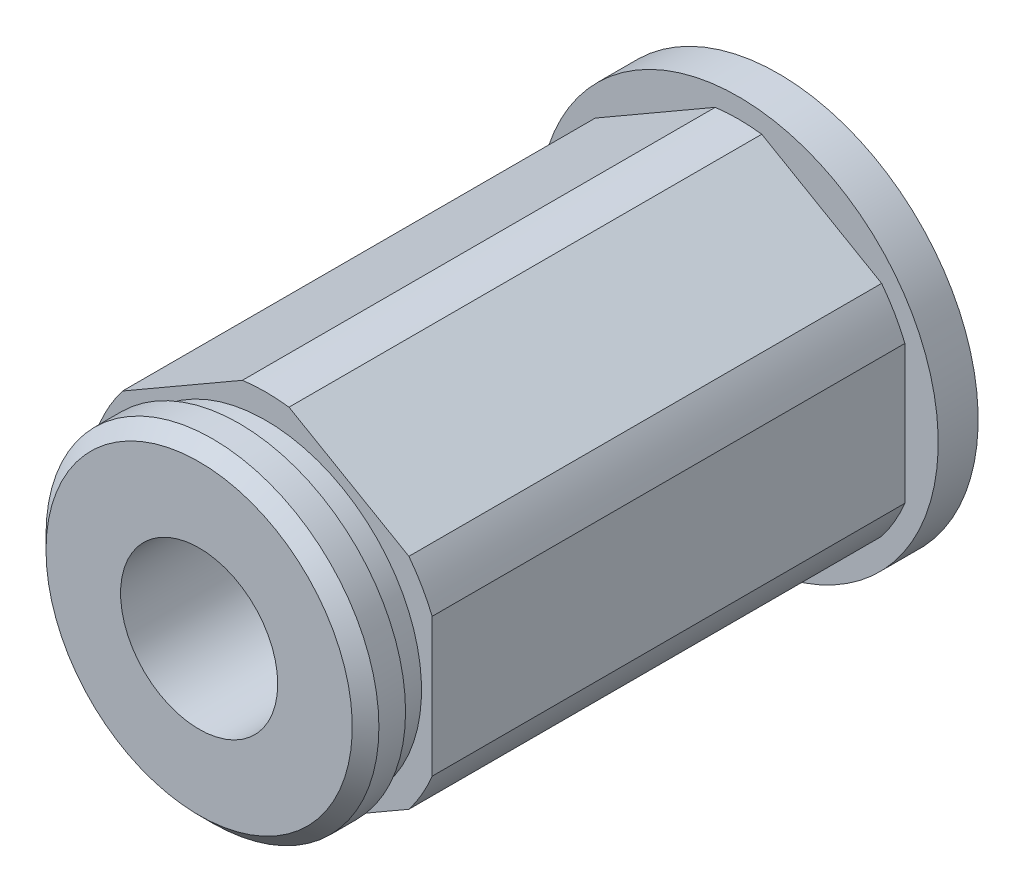
SolidWorks part; units mm, degrees
material "ThunderHex"
ref_plane "Front Plane" through (0, 0, 0) normal (0, 0, 1) x (1, 0, 0)
ref_plane "Top Plane" through (0, 0, 0) normal (0, 1, 0) x (1, 0, 0)
ref_plane "Right Plane" through (0, 0, 0) normal (1, 0, 0) x (0, 0, -1)
ref_plane "End1" through (0, 0, 9.779) normal (0, 0, 1) x (1, 0, 0)
ref_plane "End2" through (0, 0, -9.779) normal (0, 0, 1) x (1, 0, 0)
sketch "Sketch1" plane through (0, 0, 0) normal (0, 0, 1) x (1, 0, 0)
  circle A0 centre (0, 0) radius 6.35
  dimension "D1" = 12.7
extrude "Basic Rod" add sketch "Sketch1" along normal up to surface (9.779 mm away) and the other way up to surface (9.779 mm away) up to plane "End1" other way up to plane "End2"
ref_axis "Center Axis" through (0, 0, -38.2778) along (0, 0, 1)
sketch "Sketch8" plane through (0, 0, 0) normal (0, 0, 1) x (1, 0, 0)
  line L0 (-5.4616, 4.1791) -> (-6.35, 3.6662) construction
  line L1 (-0.8884, 6.8194) -> (-5.4616, 4.1791)
  line L2 (-6.35, 2.6403) -> (-6.35, -2.6403)
  line L3 (-5.4616, -4.1791) -> (-0.8884, -6.8194)
  line L4 (0.8884, -6.8194) -> (5.4616, -4.1791)
  line L5 (6.35, -2.6403) -> (6.35, 2.6403)
  line L6 (5.4616, 4.1791) -> (0.8884, 6.8194)
  line L7 (-6.35, 3.6662) -> (-6.35, 2.6403) construction
  line L8 (0, 7.3323) -> (-0.8884, 6.8194) construction
  line L9 (0.8884, 6.8194) -> (0, 7.3323) construction
  line L10 (6.35, 3.6662) -> (5.4616, 4.1791) construction
  line L11 (6.35, 2.6403) -> (6.35, 3.6662) construction
  line L12 (6.35, -3.6662) -> (6.35, -2.6403) construction
  line L13 (5.4616, -4.1791) -> (6.35, -3.6662) construction
  line L14 (0, -7.3323) -> (0.8884, -6.8194) construction
  line L15 (-0.8884, -6.8194) -> (0, -7.3323) construction
  line L16 (-6.35, -3.6662) -> (-5.4616, -4.1791) construction
  line L17 (-6.35, -2.6403) -> (-6.35, -3.6662) construction
  circle A0 centre (0, 0) radius 6.35 construction
  arc A1 (-6.35, -2.6403) -> (-5.4616, -4.1791) centre (0, 0) ccw
  circle A2 centre (0, 0) radius 6.35 construction
  arc A3 (-6.35, 2.6403) -> (-6.35, -2.6403) centre (0, 0) ccw construction
  arc A4 (-0.8884, 6.8194) -> (-5.4616, 4.1791) centre (0, 0) ccw construction
  arc A5 (-5.4616, 4.1791) -> (-6.35, 2.6403) centre (0, 0) ccw
  arc A6 (5.4616, 4.1791) -> (0.8884, 6.8194) centre (0, 0) ccw construction
  arc A7 (0.8884, 6.8194) -> (-0.8884, 6.8194) centre (0, 0) ccw
  arc A8 (6.35, -2.6403) -> (6.35, 2.6403) centre (0, 0) ccw construction
  arc A9 (6.35, 2.6403) -> (5.4616, 4.1791) centre (0, 0) ccw
  arc A10 (0.8884, -6.8194) -> (5.4616, -4.1791) centre (0, 0) ccw construction
  arc A11 (5.4616, -4.1791) -> (6.35, -2.6403) centre (0, 0) ccw
  arc A12 (-5.4616, -4.1791) -> (-0.8884, -6.8194) centre (0, 0) ccw construction
  arc A13 (-0.8884, -6.8194) -> (0.8884, -6.8194) centre (0, 0) ccw
  dimension "D1" = 13.7541
extrude "THex" add sketch "Sketch8" along normal mid plane 19.558
sketch "Sketch5" plane through (0, 0, 0) normal (0, 0, 1) x (1, 0, 0)
  line L1 (-3.6662, 6.35) -> (-7.3323, 0)
  line L2 (-7.3323, 0) -> (-3.6662, -6.35)
  line L3 (-3.6662, -6.35) -> (3.6662, -6.35)
  line L4 (3.6662, -6.35) -> (7.3323, 0)
  line L5 (7.3323, 0) -> (3.6662, 6.35)
  line L6 (3.6662, 6.35) -> (-3.6662, 6.35)
  circle A0 centre (0, 0) radius 6.35 construction
  circle A2 centre (0, 0) radius 6.35 construction
extrude "Hex" [suppressed] add sketch "Sketch5" along normal mid plane 19.558
sketch "Sketch7" plane through (0, 0, 0) normal (1, 0, 0) x (0, 0, -1)
  line L0 (0, 0) -> (-50000, 0) construction
  line L1 (-9.779, 5.9436) -> (-10.795, 5.9436)
  line L2 (-10.795, 5.9436) -> (-10.795, 6.35)
  line L3 (-10.795, 6.35) -> (-11.811, 6.35)
  line L4 (-12.319, 5.842) -> (-12.319, 0)
  line L5 (-12.319, 0) -> (-9.779, 0)
  line L6 (-9.779, 0) -> (-9.779, 5.9436)
  line L7 (-11.811, 6.35) -> (-12.319, 5.842)
  line L8 (38.2778, 0) -> (-38.2778, 0) construction
  line L9 (-9.779, 5.2388) -> (-9.779, -5.2388) construction
  point P7 (-12.319, 6.35)
  dimension "D1" = 12.7
  dimension "D4" = 1.016
  dimension "D2" = 0.4064
  dimension "D3" = 2.54
revolve "1stSnapRing" add sketch "Sketch7" angle 360 about axis through (0, 0, -38.2778) along (0, 0, 1)
mirror "2ndSnapRing" [suppressed] about plane through (0, 0, 0) normal (0, 0, 1)
sketch "Sketch2" plane through (0, 0, 0) normal (0, 0, 1) x (1, 0, 0)
  circle A0 centre (0, 0) radius 2.9972
  dimension "D1" = 5.9944
extrude "Internal Cut" cut sketch "Sketch2" against normal through all both and the other way through all
sketch "Sketch9" plane through (0, 0, -9.779) normal (0, 0, -1) x (-1, 0, 0)
  circle A0 centre (0, 0) radius 7.62
  circle A1 centre (0, 0) radius 2.9972 construction
  circle A2 centre (0, 0) radius 2.9972
  dimension "D1" = 15.24
extrude "Boss-Extrude1" add sketch "Sketch9" against normal blind 1.524
equation "\"Unit Measure\"= \"Length\"'in"
equation "\"D1@Sketch1\"=\"OD\""
equation "\"D1\"= \"Length\""
equation "\"D1@Sketch2\"=\"ID\""
equation "\"Internal Cut\"= IIF ( \"ID\" = 0 ,  suppressed  ,  unsuppressed  ) "
equation "\"D1@Hex\" = \"Length\""
equation "\"Hex\" = IIF ( \"SelectionType\" = 1 , \"suppressed\" , iif ( \"SelectionType\" = 2 , \"suppressed\" , \"unsuppressed\" ) )"
equation "\"OutsideDiameter\"= \"OD\"'in"
equation "\"ThunderHexDia\"= iif ( \"OD\" < .36 , \"OD\" * 1.1 , iif ( \"OD\" < .40 , .4035 , iif ( \"OD\" < .52 , .5415 , \"OD\" * 1.1 ) ) )"
equation "\"D1@Sketch7\"=\"Thickness\""
equation "\"SRDia\"= iif ( \"OD\" = .5 , ( \"OD\" - .468 ) / 2 , iif ( \"OD\" = .375 , ( \"OD\" - .352 ) / 2 , .050 ) )"
equation "\"D2@Sketch7\"= \"SnapRingDepth\""
equation "\"1stSnapRing\"= iif ( \"SnapRingCount\" > 0 , \"unsuppressed\" , \"suppressed\" )"
equation "\"2ndSnapRing\"= iif ( \"SnapRingCount\" = 2 , \"unsuppressed\" , \"suppressed\" )"
equation "\"D1@End1\" = \"Length\" / 2"
equation "\"D1@End2\" = \"Length\""
equation "\"D1@Sketch8\"=\"ThunderHexDia\""
equation "\"D1@THex\" = \"Length\""
equation "\"THex\"= IIF ( \"SelectionType\" = 0 ,  suppressed  , iif ( \"SelectionType\" = 2 ,  suppressed  ,  unsuppressed  )  ) "
